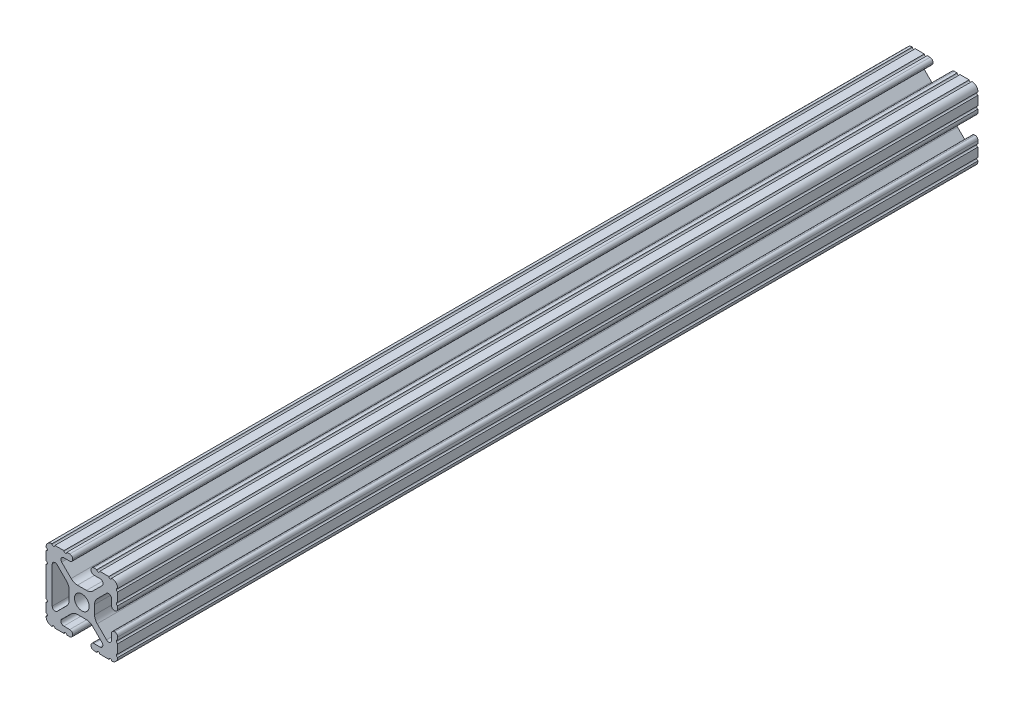
SolidWorks part; units mm, degrees
material "6061-T6 (SS)"
ref_plane "Front Plane" through (0, 0, 0) normal (0, 0, 1) x (1, 0, 0)
ref_plane "Top Plane" through (0, 0, 0) normal (0, 1, 0) x (1, 0, 0)
ref_plane "Right Plane" through (0, 0, 0) normal (1, 0, 0) x (0, 0, -1)
ref_plane "Plane1" through (0, 0, -304.8) normal (0, 0, -1) x (-1, 0, 0)
sketch "Sketch1" plane through (0, 0, -304.8) normal (0, 0, -1) x (-1, 0, 0)
  line L0 (6.4164, -10.4902) -> (4.2875, -10.4902)
  line L1 (3.2385, -11.5392) -> (3.2385, -11.651)
  line L2 (4.2875, -12.7) -> (5.3171, -12.7)
  line L3 (6.3331, -12.7) -> (9.5504, -12.7)
  line L4 (12.7, -9.5504) -> (12.7, -6.3331)
  line L5 (12.7, -5.3171) -> (12.7, 5.3171)
  line L6 (12.7, 6.3331) -> (12.7, 9.5504)
  line L7 (9.5504, 12.7) -> (6.3331, 12.7)
  line L8 (5.3171, 12.7) -> (4.2875, 12.7)
  line L9 (3.2384, 11.651) -> (3.2384, 11.5392)
  line L10 (4.2875, 10.4902) -> (6.4164, 10.4902)
  line L11 (7.1341, 8.7551) -> (3.7966, 5.4237)
  line L12 (1.5536, 4.4958) -> (-1.6573, 4.4958)
  line L13 (-3.9003, 5.4237) -> (-7.2072, 8.7245)
  line L14 (-6.4768, 10.4902) -> (-4.2875, 10.4902)
  line L15 (-3.2384, 11.5392) -> (-3.2384, 11.651)
  line L16 (-4.2875, 12.7) -> (-5.3171, 12.7)
  line L17 (-6.3331, 12.7) -> (-9.5504, 12.7)
  line L18 (-12.7, 9.5504) -> (-12.7, 6.3331)
  line L19 (-12.7, 5.3171) -> (-12.7, 4.2875)
  line L20 (-11.651, 3.2385) -> (-11.5392, 3.2385)
  line L21 (-10.4902, 4.2875) -> (-10.4902, 6.4021)
  line L22 (-8.737, 7.1292) -> (-5.4405, 3.8388)
  line L23 (-4.5085, 1.5917) -> (-4.5085, -1.5917)
  line L24 (-5.4405, -3.8388) -> (-8.737, -7.1292)
  line L25 (-10.4902, -6.4021) -> (-10.4902, -4.2875)
  line L26 (-11.5392, -3.2385) -> (-11.651, -3.2385)
  line L27 (-12.7, -4.2875) -> (-12.7, -5.3171)
  line L28 (-12.7, -6.3331) -> (-12.7, -9.5504)
  line L29 (-9.5504, -12.7) -> (-6.3331, -12.7)
  line L30 (-5.3171, -12.7) -> (-4.2875, -12.7)
  line L31 (-3.2385, -11.651) -> (-3.2385, -11.5392)
  line L32 (-4.2875, -10.4902) -> (-6.4083, -10.4902)
  line L33 (-7.1285, -8.7494) -> (-3.7967, -5.4237)
  line L34 (-1.5536, -4.4958) -> (1.5536, -4.4958)
  line L35 (3.7967, -5.4237) -> (7.1342, -8.7551)
  line L36 (10.4902, 6.4464) -> (10.4902, -6.4254)
  line L37 (8.7534, -7.1457) -> (5.4405, -3.8388)
  line L38 (4.5085, -1.5917) -> (4.5085, 1.5917)
  line L39 (5.4405, 3.8388) -> (8.7683, 7.1606)
  arc A0 (4.2875, -10.4902) -> (3.2385, -11.5392) centre (4.2875, -11.5392) ccw
  arc A1 (3.2385, -11.651) -> (4.2875, -12.7) centre (4.2875, -11.651) ccw
  arc A2 (5.3171, -12.7) -> (6.3331, -12.7) centre (5.8251, -12.7) cw
  arc A3 (9.5504, -12.7) -> (10.5664, -12.6998) centre (10.0584, -12.7) cw
  arc A4 (10.5664, -12.6998) -> (12.6998, -10.5664) centre (10.5918, -10.5918) ccw
  arc A5 (12.6998, -10.5664) -> (12.7, -9.5504) centre (12.7, -10.0584) cw
  arc A6 (12.7, -6.3331) -> (12.7, -5.3171) centre (12.7, -5.8251) cw
  arc A7 (12.7, 5.3171) -> (12.7, 6.3331) centre (12.7, 5.8251) cw
  arc A8 (12.7, 9.5504) -> (12.6998, 10.5664) centre (12.7, 10.0584) cw
  arc A9 (12.6998, 10.5664) -> (10.5664, 12.6998) centre (10.5918, 10.5918) ccw
  arc A10 (10.5664, 12.6998) -> (9.5504, 12.7) centre (10.0584, 12.7) cw
  arc A11 (6.3331, 12.7) -> (5.3171, 12.7) centre (5.8251, 12.7) cw
  arc A12 (4.2875, 12.7) -> (3.2384, 11.651) centre (4.2875, 11.651) ccw
  arc A13 (3.2384, 11.5392) -> (4.2875, 10.4902) centre (4.2875, 11.5392) ccw
  arc A14 (6.4164, 10.4902) -> (7.1341, 8.7551) centre (6.4164, 9.4742) cw
  arc A15 (3.7966, 5.4237) -> (1.5536, 4.4958) centre (1.5536, 7.6708) cw
  arc A16 (-1.6573, 4.4958) -> (-3.9003, 5.4237) centre (-1.6573, 7.6708) cw
  arc A17 (-7.2072, 8.7245) -> (-6.4768, 10.4902) centre (-6.4768, 9.4563) cw
  arc A18 (-4.2875, 10.4902) -> (-3.2384, 11.5392) centre (-4.2875, 11.5392) ccw
  arc A19 (-3.2384, 11.651) -> (-4.2875, 12.7) centre (-4.2875, 11.651) ccw
  arc A20 (-5.3171, 12.7) -> (-6.3331, 12.7) centre (-5.8251, 12.7) cw
  arc A21 (-9.5504, 12.7) -> (-10.5664, 12.6998) centre (-10.0584, 12.7) cw
  arc A22 (-10.5664, 12.6998) -> (-12.6998, 10.5664) centre (-10.5918, 10.5918) ccw
  arc A23 (-12.6998, 10.5664) -> (-12.7, 9.5504) centre (-12.7, 10.0584) cw
  arc A24 (-12.7, 6.3331) -> (-12.7, 5.3171) centre (-12.7, 5.8251) cw
  arc A25 (-12.7, 4.2875) -> (-11.651, 3.2385) centre (-11.651, 4.2875) ccw
  arc A26 (-11.5392, 3.2385) -> (-10.4902, 4.2875) centre (-11.5392, 4.2875) ccw
  arc A27 (-10.4902, 6.4021) -> (-8.737, 7.1292) centre (-9.4628, 6.4021) cw
  arc A28 (-5.4405, 3.8388) -> (-4.5085, 1.5917) centre (-7.6835, 1.5917) cw
  arc A29 (-4.5085, -1.5917) -> (-5.4405, -3.8388) centre (-7.6835, -1.5917) cw
  arc A30 (-8.737, -7.1292) -> (-10.4902, -6.4021) centre (-9.4628, -6.4021) cw
  arc A31 (-10.4902, -4.2875) -> (-11.5392, -3.2385) centre (-11.5392, -4.2875) ccw
  arc A32 (-11.651, -3.2385) -> (-12.7, -4.2875) centre (-11.651, -4.2875) ccw
  arc A33 (-12.7, -5.3171) -> (-12.7, -6.3331) centre (-12.7, -5.8251) cw
  arc A34 (-12.7, -9.5504) -> (-12.6998, -10.5664) centre (-12.7, -10.0584) cw
  arc A35 (-12.6998, -10.5664) -> (-10.5664, -12.6998) centre (-10.5918, -10.5918) ccw
  arc A36 (-10.5664, -12.6998) -> (-9.5504, -12.7) centre (-10.0584, -12.7) cw
  arc A37 (-6.3331, -12.7) -> (-5.3171, -12.7) centre (-5.8251, -12.7) cw
  arc A38 (-4.2875, -12.7) -> (-3.2385, -11.651) centre (-4.2875, -11.651) ccw
  arc A39 (-3.2385, -11.5392) -> (-4.2875, -10.4902) centre (-4.2875, -11.5392) ccw
  arc A40 (-6.4083, -10.4902) -> (-7.1285, -8.7494) centre (-6.4083, -9.4709) cw
  arc A41 (-3.7967, -5.4237) -> (-1.5536, -4.4958) centre (-1.5536, -7.6708) cw
  arc A42 (1.5536, -4.4958) -> (3.7967, -5.4237) centre (1.5536, -7.6708) cw
  arc A43 (7.1342, -8.7551) -> (6.4164, -10.4902) centre (6.4164, -9.4742) cw
  arc A44 (8.7683, 7.1606) -> (10.4902, 6.4464) centre (9.4812, 6.4464) cw
  arc A45 (10.4902, -6.4254) -> (8.7534, -7.1457) centre (9.4724, -6.4254) cw
  arc A46 (5.4405, -3.8388) -> (4.5085, -1.5917) centre (7.6835, -1.5917) cw
  arc A47 (4.5085, 1.5917) -> (5.4405, 3.8388) centre (7.6835, 1.5917) cw
  circle A48 centre (0, 0) radius 2.6035
extrude "Boss-Extrude1" add sketch "Sketch1" against normal blind 304.8
